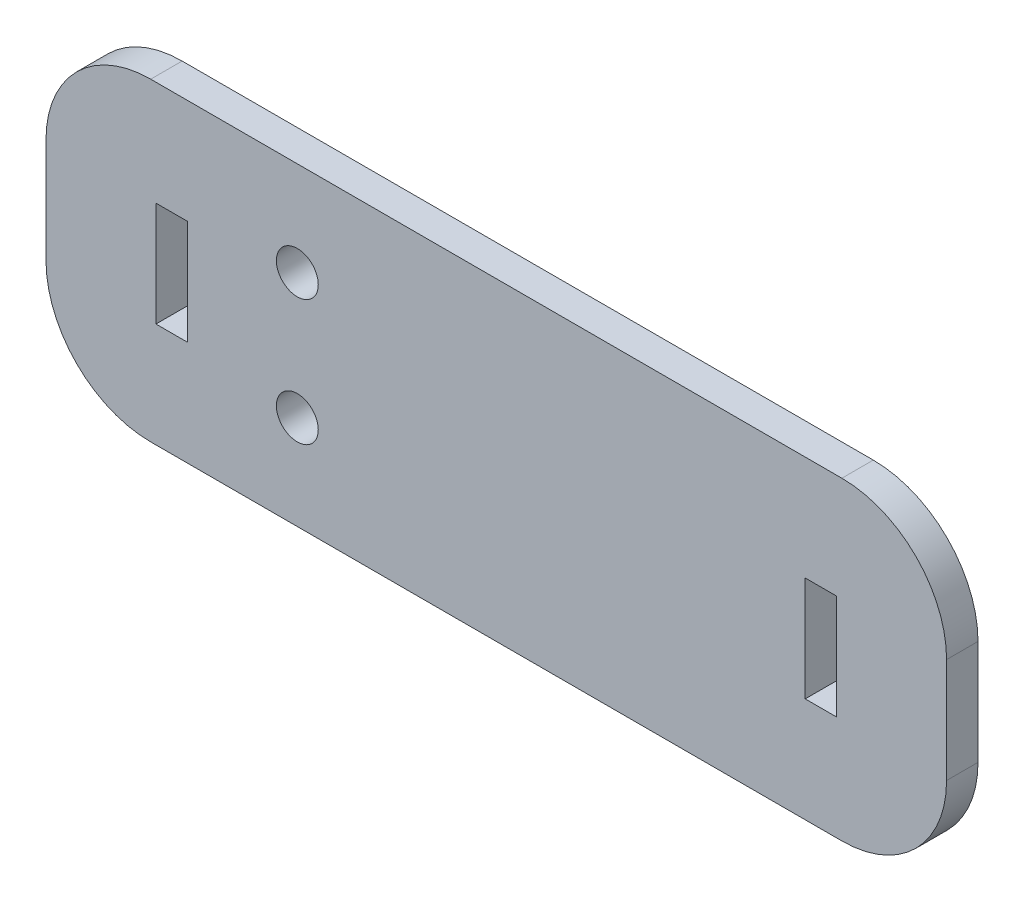
SolidWorks part; units mm, degrees
material "Balsa"
ref_plane "Alzado" through (0, 0, 0) normal (0, 0, 1) x (1, 0, 0)
ref_plane "Planta" through (0, 0, 0) normal (0, 1, 0) x (1, 0, 0)
ref_plane "Vista lateral" through (0, 0, 0) normal (1, 0, 0) x (0, 0, -1)
sketch "Croquis1" plane through (0, 0, 0) normal (0, 0, 1) x (1, 0, 0)
  line L1 (-43, 15) -> (43, 15)
  line L2 (-43, 15) -> (-43, -15)
  line L3 (-43, -15) -> (43, -15)
  line L4 (43, 15) -> (43, -15)
  line L5 (-43, 15) -> (43, -15) construction
  line L6 (-43, -15) -> (43, 15) construction
  point P0 (0, 0)
  dimension "D1" = 30
  dimension "D2" = 86
extrude "Saliente-Extruir1" add sketch "Croquis1" along normal blind 3
sketch "Croquis2" plane through (0, 0, 3) normal (0, 0, 1) x (1, 0, 0)
  line L0 (-43, -15) -> (43, -15) construction
  line L1 (-32.5, 5) -> (-29.5, 5)
  line L2 (-32.5, 5) -> (-32.5, -5)
  line L3 (-32.5, -5) -> (-29.5, -5)
  line L4 (-29.5, 5) -> (-29.5, -5)
  line L5 (-32.5, 5) -> (-29.5, -5) construction
  line L6 (-32.5, -5) -> (-29.5, 5) construction
  line L7 (-43, 15) -> (-43, -15) construction
  line L8 (0, 0) -> (0, -3.9173) construction
  line L9 (32.5, -5) -> (29.5, 5) construction
  line L10 (32.5, 5) -> (29.5, -5) construction
  line L11 (29.5, 5) -> (29.5, -5)
  line L12 (32.5, -5) -> (29.5, -5)
  line L13 (32.5, 5) -> (32.5, -5)
  line L14 (32.5, 5) -> (29.5, 5)
  circle A0 centre (-19, 6) radius 2
  circle A1 centre (-19, -6) radius 2
  point P0 (-31, 0)
  point P16 (31, 0)
  dimension "D5" = 4
  dimension "D6" = 4
  dimension "D1" = 3
  dimension "D2" = 10
  dimension "D3" = 15
  dimension "D4" = 12
  dimension "D7" = 24
  dimension "D8" = 24
  dimension "D9" = 12
  dimension "D10" = 6
extrude "Cortar-Extruir1" cut sketch "Croquis2" against normal up to next
fillet "Redondeo1" radius 10 4 edges at (43, -15, 1.5) (43, 15, 1.5) (-43, -15, 1.5) (-43, 15, 1.5)
